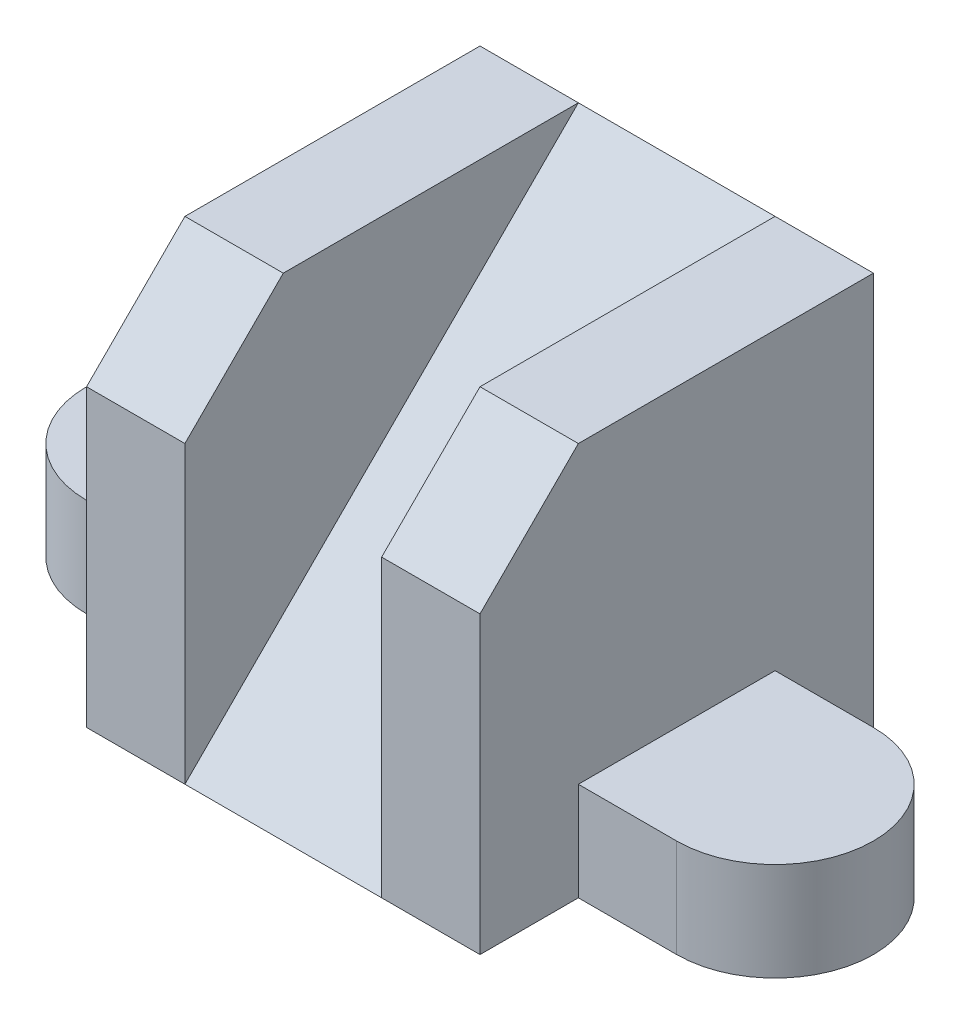
SolidWorks part; units mm, degrees
material "회주철"
ref_plane "정면" through (0, 0, 0) normal (0, 0, 1) x (1, 0, 0)
ref_plane "윗면" through (0, 0, 0) normal (0, 1, 0) x (1, 0, 0)
ref_plane "우측면" through (0, 0, 0) normal (1, 0, 0) x (0, 0, -1)
sketch "스케치1" plane through (0, 0, 0) normal (1, 0, 0) x (0, 0, -1)
  line L0 (14, 0) -> (-14, 0)
  line L1 (-14, 0) -> (-14, 21)
  line L2 (-7, 28) -> (14, 28)
  line L3 (14, 28) -> (14, 0)
  line L4 (-14, 21) -> (-7, 28)
  point P3 (-14, 28)
  dimension "D1" = 28
  dimension "D2" = 28
extrude "보스-돌출1" add sketch "스케치1" along normal mid plane 28
sketch "스케치2" plane through (0, 0, 0) normal (1, 0, 0) x (0, 0, -1)
  line L0 (-14, 0) -> (14, 28)
  line L1 (14, 28) -> (-14, 28)
  line L2 (-14, 28) -> (-14, 0)
  dimension "D1" = 28
  dimension "D2" = 28
extrude "컷-돌출1" cut sketch "스케치2" against normal mid plane 14
sketch "스케치3" plane through (0, 0, 0) normal (0, 1, 0) x (1, 0, 0)
  line L0 (0, 0) -> (0, 14) construction
  line L1 (-21, 7) -> (-14, 7)
  line L2 (-14, 14) -> (-14, -7) construction
  line L3 (-21, -7) -> (-14, -7)
  line L4 (-14, 7) -> (-14, -7)
  line L5 (-7, 14) -> (7, 14) construction
  line L6 (14, 7) -> (14, -7)
  line L7 (21, -7) -> (14, -7)
  line L8 (21, 7) -> (14, 7)
  arc A0 (-21, 7) -> (-21, -7) centre (-21, 0) ccw
  arc A1 (21, 7) -> (21, -7) centre (21, 0) cw
  dimension "D1" = 7
  dimension "D2" = 42
extrude "보스-돌출2" add sketch "스케치3" along normal blind 7
